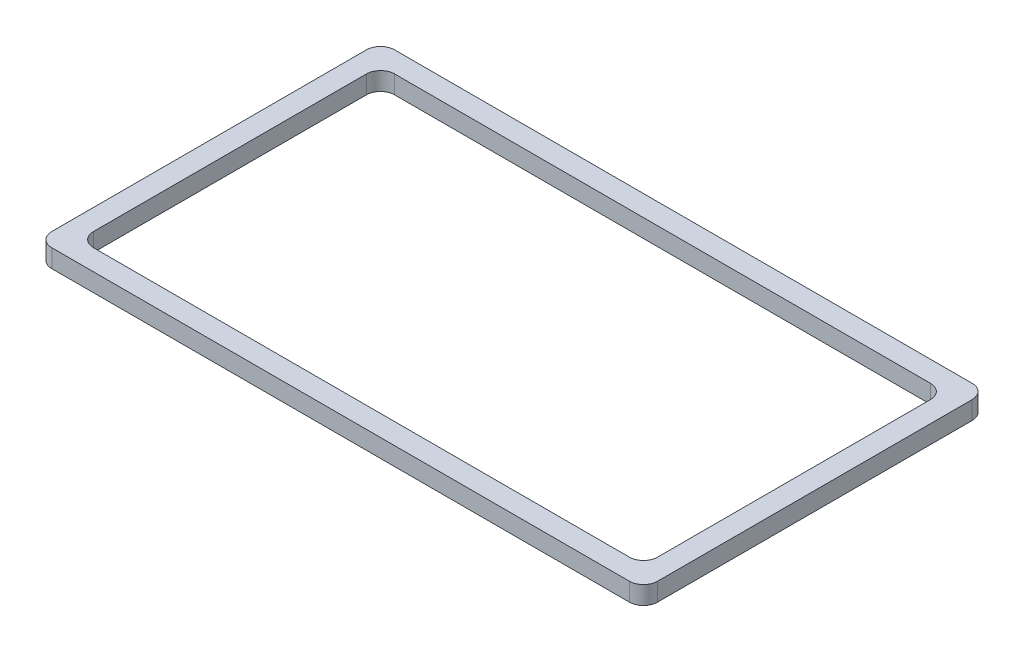
SolidWorks part; units mm, degrees
ref_plane "Front Plane" through (0, 0, 0) normal (0, 0, 1) x (1, 0, 0)
ref_plane "Top Plane" through (0, 0, 0) normal (0, 1, 0) x (1, 0, 0)
ref_plane "Right Plane" through (0, 0, 0) normal (1, 0, 0) x (0, 0, -1)
sketch "Sketch1" plane through (0, 0, 0) normal (0, 1, 0) x (1, 0, 0)
  line L0 (33.4, 37.8) -> (33.4, 35.5) construction
  line L1 (0, 0) -> (66.8, 0)
  line L2 (0, 0) -> (0, 37.8)
  line L3 (0, 37.8) -> (66.8, 37.8)
  line L4 (66.8, 0) -> (66.8, 37.8)
  line L5 (2.3, 2.3) -> (64.5, 2.3)
  line L6 (2.3, 2.3) -> (2.3, 35.5)
  line L7 (2.3, 35.5) -> (64.5, 35.5)
  line L8 (64.5, 2.3) -> (64.5, 35.5)
  line L9 (33.4, 2.3) -> (33.4, 0) construction
  line L10 (0, 18.9) -> (2.3, 18.9) construction
  line L11 (64.5, 18.9) -> (66.8, 18.9) construction
  dimension "D1" = 2.3
  dimension "D2" = 62.2
  dimension "D5" = 33.2
extrude "Boss-Extrude1" add sketch "Sketch1" along normal blind 2
fillet "Fillet1" radius 1.55 8 edges at (64.5, 1, -35.5) (66.8, 1, -37.8) (66.8, 1, 0) (64.5, 1, -2.3) (2.3, 1, -2.3) (0, 1, -37.8) (2.3, 1, -35.5) (0, 1, 0)
